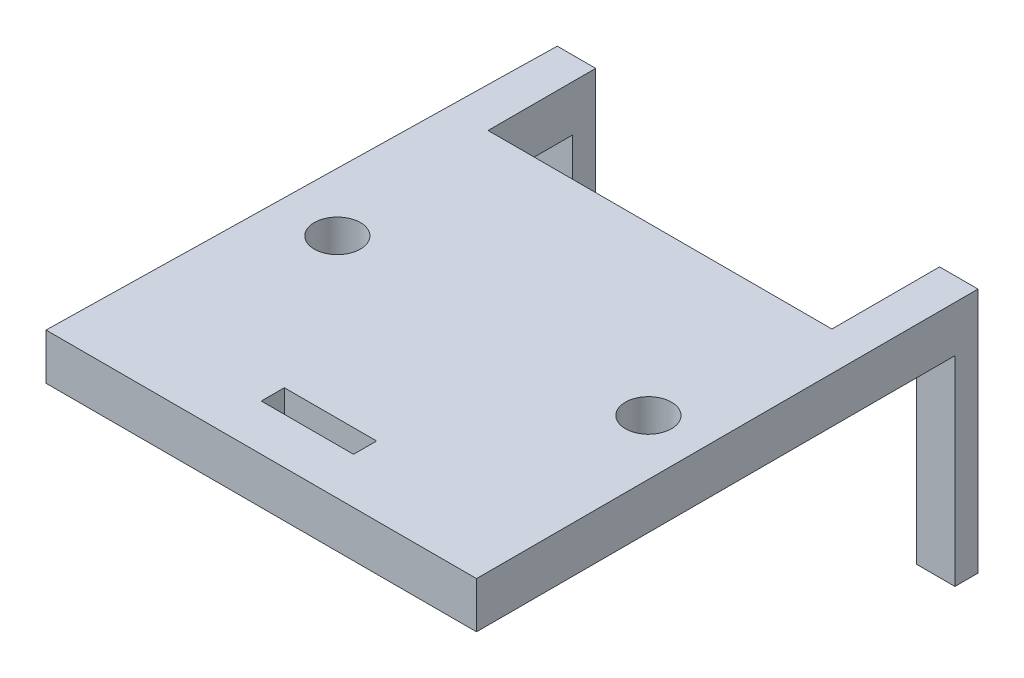
SolidWorks part; units mm, degrees
ref_plane "Front Plane" through (0, 0, 0) normal (0, 0, 1) x (1, 0, 0)
ref_plane "Top Plane" through (0, 0, 0) normal (0, 1, 0) x (1, 0, 0)
ref_plane "Right Plane" through (0, 0, 0) normal (1, 0, 0) x (0, 0, -1)
sketch "Sketch1" plane through (0, 0, 0) normal (0, 1, 0) x (1, 0, 0)
  line L0 (2.6366, -0.0013) -> (25, -0.0013)
  line L1 (27.5, 0.0049) -> (27.5, -25.6136)
  line L2 (27.5, -25.6136) -> (-0.5, -25.6136)
  line L3 (-0.5, -25.6136) -> (0, 0)
  line L4 (0, 0) -> (0.1366, 6.9987)
  line L7 (27.5, 6.9987) -> (25, 6.9987)
  line L8 (25, 6.9987) -> (25, -0.0013)
  line L9 (0.1366, 6.9987) -> (2.6366, 6.9987)
  line L11 (2.6366, 6.9987) -> (2.6366, -0.0013)
  line L12 (27.5, 6.9987) -> (27.5, 0.0049)
  dimension "D6" = 7
  dimension "D1" = 27.5
  dimension "D2" = 28
  dimension "D3" = 25.6123
  dimension "D4" = 2.5
  dimension "D5" = 2.5
  dimension "D7" = 7
extrude "Boss-Extrude1" add sketch "Sketch1" along normal blind 3
sketch "Sketch2" plane through (0, 0, 0) normal (0, -1, 0) x (-1, 0, 0)
  line L6 (-2.6366, 6.9987) -> (-0.1366, 6.9987)
  line L7 (-0.1366, 6.9987) -> (-0.1073, 5.4987)
  line L8 (-0.1366, 6.9987) -> (0.5, -25.6136) construction
  line L9 (-0.1073, 5.4987) -> (-2.6366, 5.4987)
  line L10 (-2.6366, -0.0013) -> (-2.6366, 6.9987) construction
  line L11 (-2.6366, 5.4987) -> (-2.6366, 6.9987)
  dimension "D1" = 1.5
extrude "Boss-Extrude2" add sketch "Sketch2" along normal blind 13
sketch "Sketch4" plane through (0, 0, 0) normal (0, -1, 0) x (-1, 0, 0)
  line L0 (-27.5, 6.9987) -> (-25, 6.9987)
  line L1 (-25, 6.9987) -> (-25, 5.4987)
  line L2 (-25, 6.9987) -> (-25, -0.0013) construction
  line L3 (-25, 5.4987) -> (-27.5, 5.4987)
  line L4 (-27.5, -25.6136) -> (-27.5, 6.9987) construction
  line L5 (-27.5, 5.4987) -> (-27.5, 6.9987)
  dimension "D1" = 1.5
extrude "Boss-Extrude3" add sketch "Sketch4" along normal blind 13
sketch "Sketch5" plane through (0, 3, 0) normal (0, 1, 0) x (1, 0, 0)
  circle A0 centre (3.6691, -10.8361) radius 1.5
  circle A1 centre (23.9026, -10.8361) radius 1.5
  dimension "D1" = 3
  dimension "D2" = 3
extrude "Cut-Extrude2" cut sketch "Sketch5" against normal blind 10
sketch "Sketch6" plane through (0, 3, 0) normal (0, 1, 0) x (1, 0, 0)
  line L0 (-0.5, -25.6136) -> (27.5, -25.6136) construction
  line L1 (10.5, -21.1136) -> (16.5, -21.1136)
  line L2 (10.5, -21.1136) -> (10.5, -22.6136)
  line L3 (10.5, -22.6136) -> (16.5, -22.6136)
  line L4 (16.5, -21.1136) -> (16.5, -22.6136)
  dimension "D1" = 1.5
  dimension "D2" = 6
  dimension "D3" = 3
extrude "Cut-Extrude3" cut sketch "Sketch6" against normal blind 10
